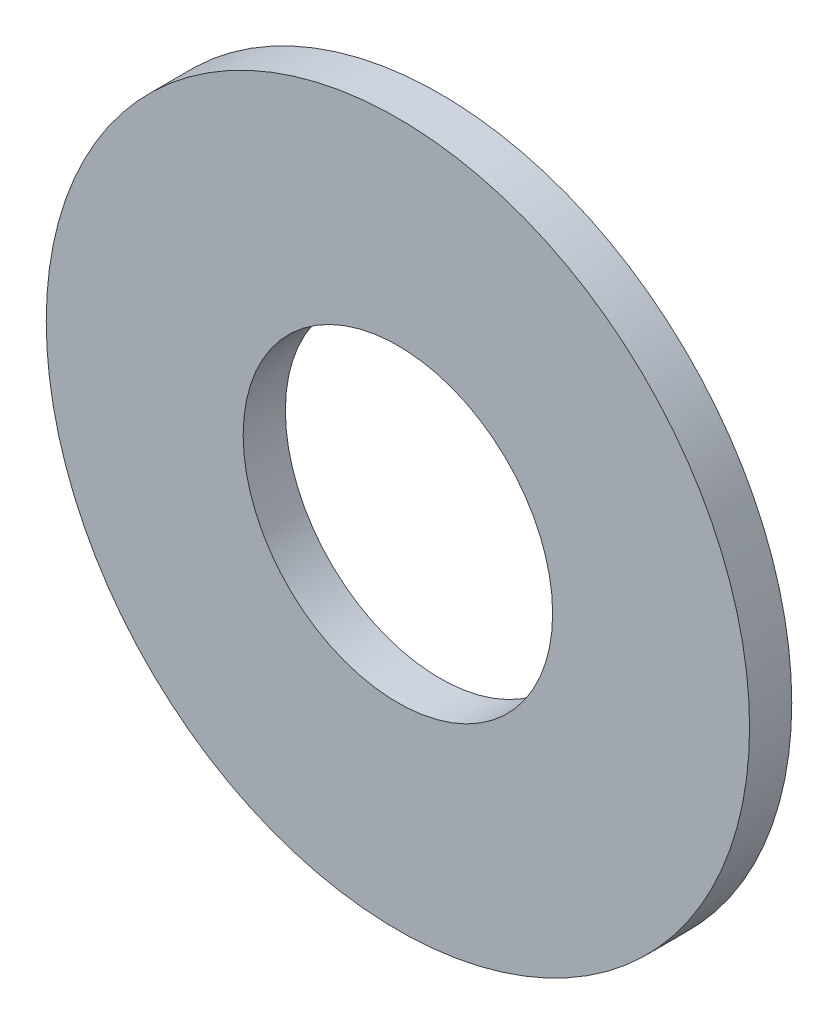
SolidWorks part; units mm, degrees
material "AISI Тип A2 Инструментальная сталь"
ref_plane "Front" through (0, 0, 0) normal (0, 0, 1) x (1, 0, 0)
ref_plane "Top" through (0, 0, 0) normal (0, 1, 0) x (1, 0, 0)
ref_plane "Right" through (0, 0, 0) normal (1, 0, 0) x (0, 0, -1)
sketch "Эскиз1" plane through (0, 0, 0) normal (0, 0, 1) x (1, 0, 0)
  circle A0 centre (0, 0) radius 2.5
  circle A1 centre (0, 0) radius 1.1
  dimension "D1" = 5
  dimension "D2" = 2.2
extrude "Бобышка-Вытянуть1" add sketch "Эскиз1" along normal blind 0.3
